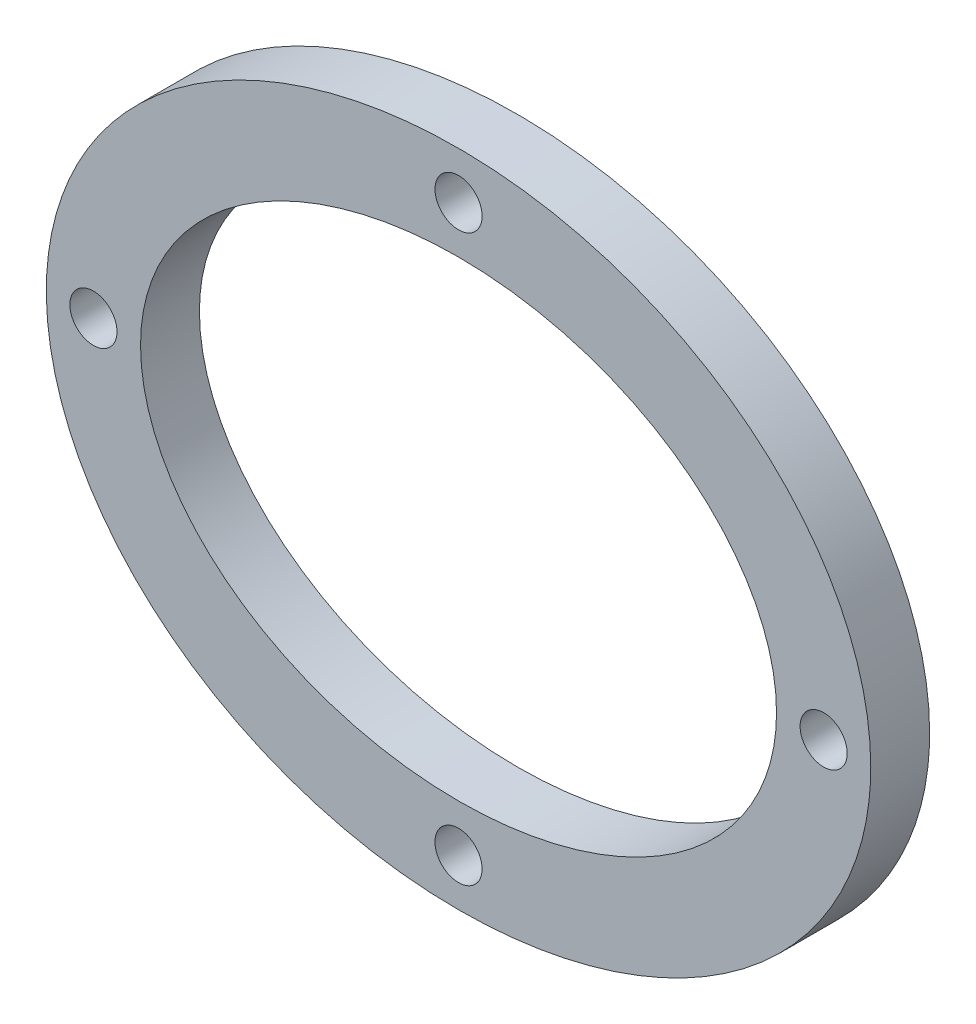
SolidWorks part; units mm, degrees
material "Balsa"
ref_plane "Plan de face" through (0, 0, 0) normal (0, 0, 1) x (1, 0, 0)
ref_plane "Plan de dessus" through (0, 0, 0) normal (0, 1, 0) x (1, 0, 0)
ref_plane "Plan de droite" through (0, 0, 0) normal (1, 0, 0) x (0, 0, -1)
sketch "Esquisse1" plane through (0, 0, 0) normal (0, 0, 1) x (1, 0, 0)
  line L0 (0, -20) -> (0, 20) construction
  line L2 (-27, 0) -> (27, 0) construction
  ellipse E0 centre (0, 0) end of major axis (27, 0) minor radius 20
  ellipse E1 centre (0, 0) end of major axis (35, 0) minor radius 28
extrude "Boss.-Extru.1" add sketch "Esquisse1" along normal blind 5
sketch "Esquisse2" plane through (0, 0, 5) normal (0, 0, 1) x (1, 0, 0)
  circle A0 centre (-31, 0) radius 2
  circle A1 centre (0, 24) radius 2
  circle A2 centre (31, 0) radius 2
  circle A3 centre (0, -24) radius 2
  dimension "D1" = 4
  dimension "D4" = 4
  dimension "D5" = 4
  dimension "D6" = 4
  dimension "D2" = 24
  dimension "D3" = 31
  dimension "D7" = 31
  dimension "D8" = 24
extrude "Enlèv. mat.-Extru.1" cut sketch "Esquisse2" against normal blind 5
